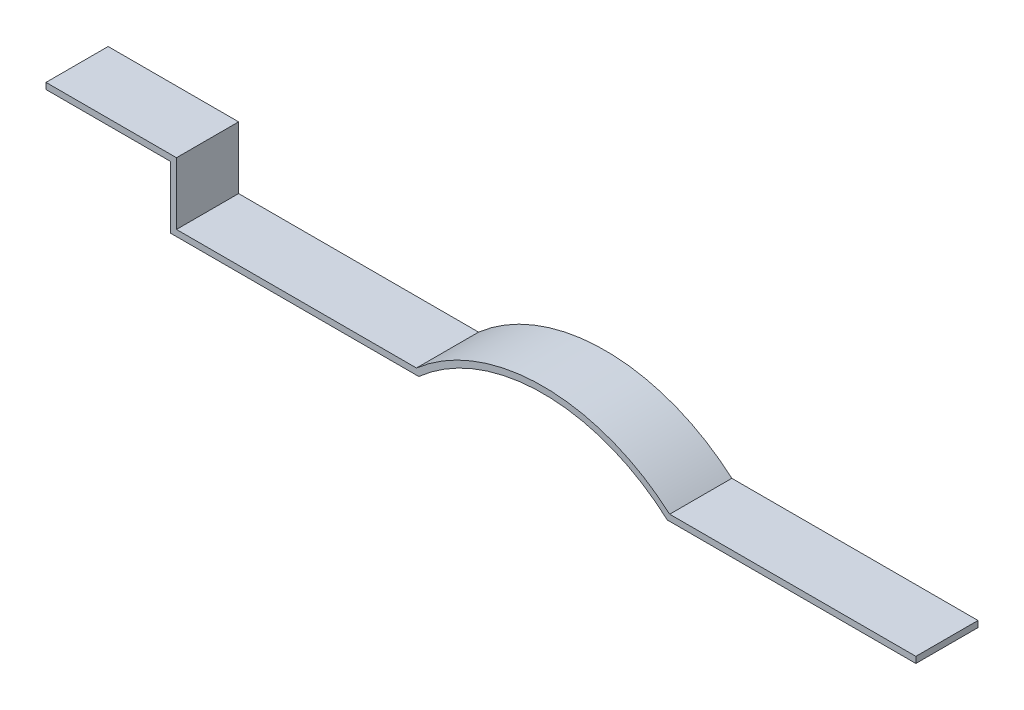
SolidWorks part; units mm, degrees
ref_plane "Front Plane" through (0, 0, 0) normal (0, 0, 1) x (1, 0, 0)
ref_plane "Top Plane" through (0, 0, 0) normal (0, 1, 0) x (1, 0, 0)
ref_plane "Right Plane" through (0, 0, 0) normal (1, 0, 0) x (0, 0, -1)
sketch "Sketch1" plane through (0, 0, 0) normal (0, 0, 1) x (1, 0, 0)
  line L0 (0, 0) -> (-200, 0)
  line L1 (-400, 0) -> (-600, 0)
  line L2 (-600, 0) -> (-600, 50)
  line L3 (-600, 50) -> (-700, 50)
  line L4 (0, 5) -> (-198.1081, 5)
  line L5 (-401.8919, 5) -> (-595, 5)
  line L6 (-595, 5) -> (-595, 55)
  line L7 (-595, 55) -> (-700, 55)
  line L8 (-700, 50) -> (-700, 55)
  line L9 (0, 5) -> (0, 0)
  arc A0 (-400, 0) -> (-200, 0) centre (-300, -111.8034) cw
  arc A1 (-401.8919, 5) -> (-198.1081, 5) centre (-300, -111.8034) cw
  dimension "D2" = 150
  dimension "D1" = 200
  dimension "D3" = 200
  dimension "D4" = 100
  dimension "D5" = 50
  dimension "D6" = 200
  dimension "D7" = 5
extrude "Boss-Extrude1" add sketch "Sketch1" along normal blind 50
